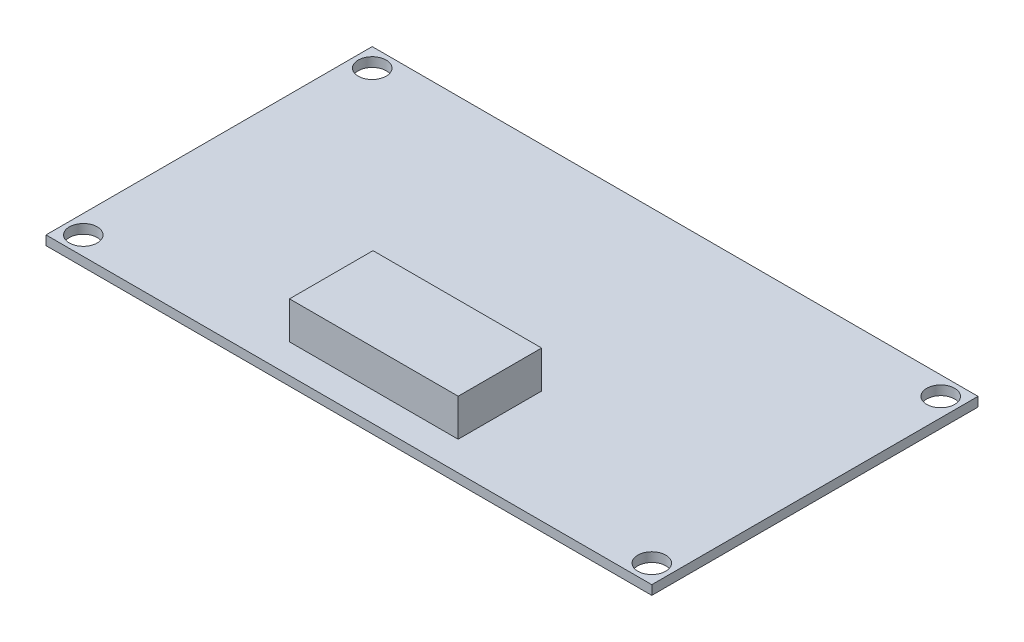
SolidWorks part; units mm, degrees
ref_plane "前视基准面" through (0, 0, 0) normal (0, 0, 1) x (1, 0, 0)
ref_plane "上视基准面" through (0, 0, 0) normal (0, 1, 0) x (1, 0, 0)
ref_plane "右视基准面" through (0, 0, 0) normal (1, 0, 0) x (0, 0, -1)
sketch "草图2" plane through (0, 0, 0) normal (0, 1, 0) x (1, 0, 0)
  line L1 (-32.5, 17.5) -> (32.5, 17.5)
  line L2 (-32.5, 17.5) -> (-32.5, -17.5)
  line L3 (-32.5, -17.5) -> (32.5, -17.5)
  line L4 (32.5, 17.5) -> (32.5, -17.5)
  line L5 (-32.5, 17.5) -> (32.5, -17.5) construction
  line L6 (-32.5, -17.5) -> (32.5, 17.5) construction
  point P0 (0, 0)
  dimension "D1" = 35
  dimension "D2" = 65
extrude "凸台-拉伸1" add sketch "草图2" along normal blind 1
hole_wizard "Ø3.0 (3) 直径孔1" positions "草图3" profile "草图4" hole size "Ø3.0" standard "GB"
sketch "草图3" plane through (0, 1, 0) normal (0, 1, 0) x (1, 0, 0)
  line L0 (49.3259, 0) -> (0, 0) construction
  line L1 (0, 0) -> (0, 27.8336) construction
  point P0 (-30.5, 15.5)
  point P2 (-30.5, -15.5)
  point P4 (30.5, -15.5)
  point P6 (30.5, 15.5)
  dimension "D1" = 31
  dimension "D2" = 61
sketch "草图4" plane through (-30.5, 1, -15.5) normal (1, 0, 0) x (0, 0, 1)
  line L0 (0, 0) -> (0, 13.3013)
  line L1 (0, 13.3013) -> (1.5, 12.4)
  line L2 (1.5, 12.4) -> (1.5, 0)
  line L5 (1.5, 0) -> (0, 0)
  line L10 (0, 13.3013) -> (-1.5, 12.4) construction
  line L11 (0, -6.35) -> (0, 107.95) construction
  dimension "孔直径" = 3
  dimension "孔深度" = 12.4
  dimension "导头角度" = 118
sketch "草图5" plane through (0, 1, 0) normal (0, 1, 0) x (1, 0, 0)
  line L1 (-9.4945, -5.419) -> (8.5988, -5.419)
  line L2 (-9.4945, -5.419) -> (-9.4945, -14.3761)
  line L3 (-9.4945, -14.3761) -> (8.5988, -14.3761)
  line L4 (8.5988, -5.419) -> (8.5988, -14.3761)
extrude "凸台-拉伸2" add sketch "草图5" along normal blind 4
